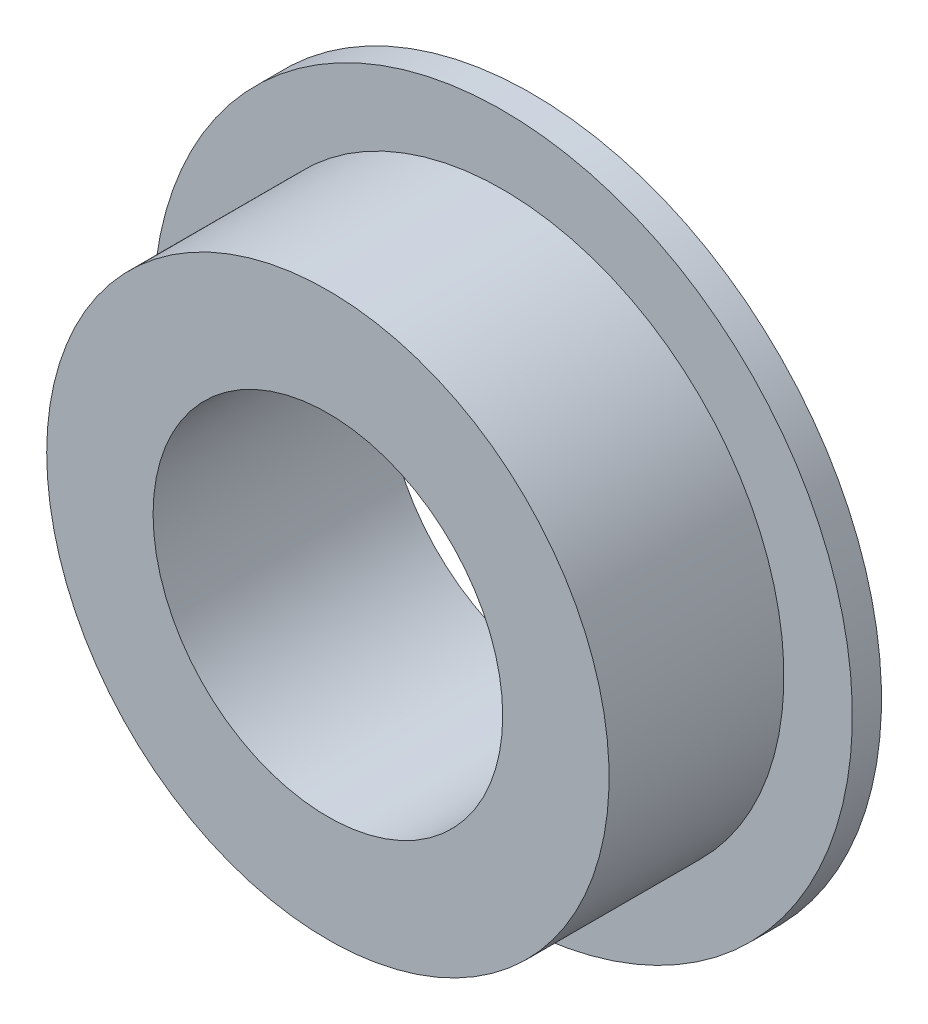
SolidWorks part; units mm, degrees
ref_plane "Front Plane" through (0, 0, 0) normal (0, 0, 1) x (1, 0, 0)
ref_plane "Top Plane" through (0, 0, 0) normal (0, 1, 0) x (1, 0, 0)
ref_plane "Right Plane" through (0, 0, 0) normal (1, 0, 0) x (0, 0, -1)
sketch "Sketch1" plane through (0, 0, 0) normal (0, 0, 1) x (1, 0, 0)
  circle A0 centre (0, 0) radius 9.525
  circle A1 centre (0, 0) radius 19.05
  dimension "D1" = 19.05
  dimension "D2" = 38.1
extrude "Boss-Extrude1" add sketch "Sketch1" along normal blind 12.7
sketch "Sketch2" plane through (0, 0, 0) normal (1, 0, 0) x (0, 0, -1)
  line L0 (0, 0) -> (-12.7, 0) construction
  line L1 (-12.7, 19.05) -> (-12.7, -19.05) construction
  line L2 (0, 12.7) -> (-1.5875, 12.7)
  line L7 (0, -19.05) -> (0, 19.05) construction
  line L8 (-1.5875, 12.7) -> (-1.5875, 19.05)
  line L9 (0, 19.05) -> (-12.7, 19.05) construction
  line L10 (-1.5875, 19.05) -> (-3.175, 19.05) construction
  line L11 (-3.175, 19.05) -> (-3.175, 15.321)
  line L12 (-3.175, 15.321) -> (-12.7, 15.321)
  line L13 (-12.7, 15.321) -> (-12.7, 19.05)
  line L14 (-12.7, 19.05) -> (-3.175, 19.05)
  line L15 (-1.5875, 19.05) -> (0, 19.05)
  line L16 (0, 19.05) -> (0, 12.7)
  dimension "D1" = 11.1125
  dimension "D2" = 30.642
  dimension "D3" = 38.1
  dimension "D4" = 12.7
revolve "Cut-Revolve1" cut sketch "Sketch2" angle 360 about L0
